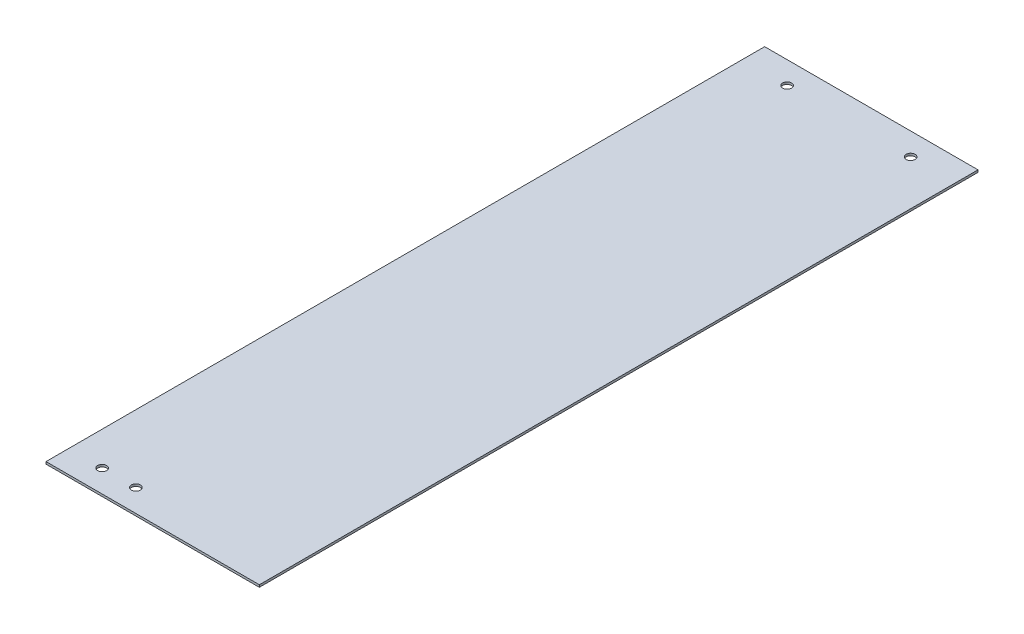
SolidWorks part; units mm, degrees
ref_plane "前视基准面" through (0, 0, 0) normal (0, 0, 1) x (1, 0, 0)
ref_plane "上视基准面" through (0, 0, 0) normal (0, 1, 0) x (1, 0, 0)
ref_plane "右视基准面" through (0, 0, 0) normal (1, 0, 0) x (0, 0, -1)
sketch "Sketch1" plane through (0, 0, 0) normal (0, 1, 0) x (1, 0, 0)
  line L0 (-47.5, 150) -> (47.5, 150) construction
  line L1 (-47.5, 160) -> (47.5, 160)
  line L2 (-47.5, 160) -> (-47.5, -160)
  line L3 (-47.5, -160) -> (47.5, -160)
  line L4 (47.5, 160) -> (47.5, -160)
  line L5 (-47.5, 160) -> (47.5, -160) construction
  line L6 (-47.5, -160) -> (47.5, 160) construction
  line L7 (0, 160) -> (0, 113.2269) construction
  circle A0 centre (-27.5, 150) radius 2
  circle A1 centre (27.5, 150) radius 2
  point P0 (0, 0)
  dimension "D2" = 4
  dimension "D4" = 20
  dimension "D1" = 95
  dimension "320" = 320
  dimension "D3" = 10
extrude "Boss-Extrude1" add sketch "Sketch1" along normal blind 1
sketch "Sketch2" plane through (0, 1, 0) normal (0, 1, 0) x (1, 0, 0)
  line L0 (-47.5, -150) -> (47.5, -150) construction
  line L1 (-47.5, 160) -> (-47.5, -160) construction
  line L2 (47.5, -160) -> (47.5, 160) construction
  line L3 (-47.5, -160) -> (47.5, -160) construction
  circle A0 centre (-32.5, -150) radius 2
  circle A1 centre (-17.5, -150) radius 2
  dimension "D2" = 15
  dimension "D3" = 15
  dimension "D4" = 4
  dimension "D5" = 4
  dimension "D1" = 10
extrude "Cut-Extrude1" cut sketch "Sketch2" against normal through all and the other way through all
